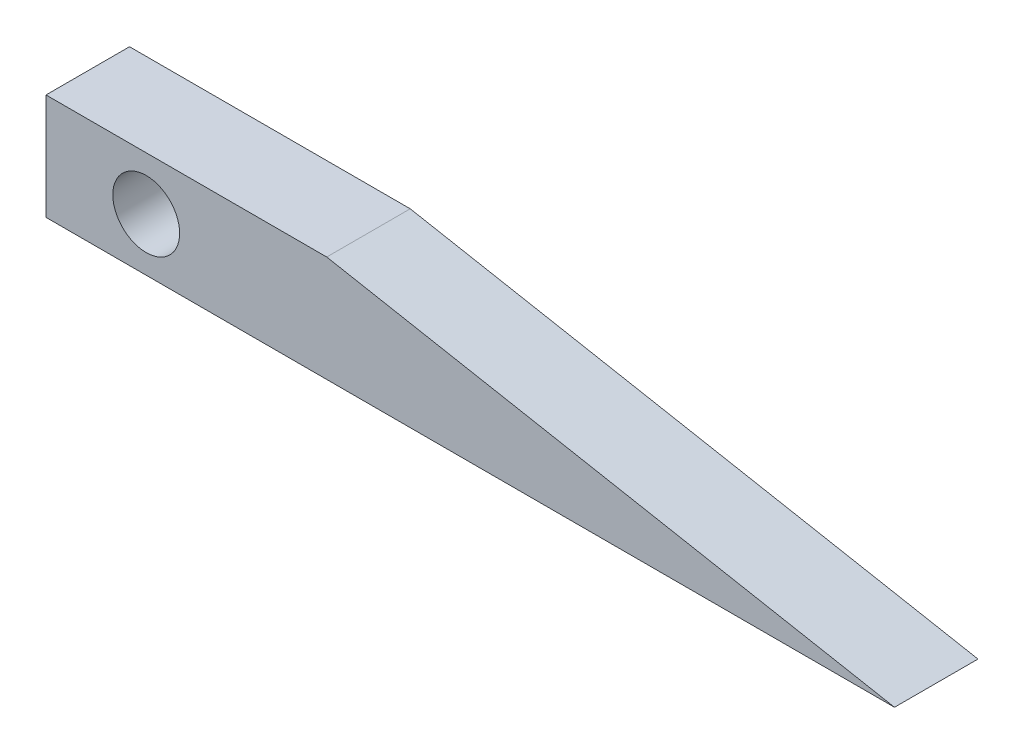
SolidWorks part; units mm, degrees
ref_plane "Front Plane" through (0, 0, 0) normal (0, 0, 1) x (1, 0, 0)
ref_plane "Top Plane" through (0, 0, 0) normal (0, 1, 0) x (1, 0, 0)
ref_plane "Right Plane" through (0, 0, 0) normal (1, 0, 0) x (0, 0, -1)
sketch "Sketch1" plane through (0, 0, 0) normal (0, 0, 1) x (1, 0, 0)
  line L5 (0, 6.35) -> (50.8, 6.35)
  line L6 (0, 6.35) -> (0, 0)
  line L7 (0, 0) -> (50.8, 0)
  line L8 (50.8, 6.35) -> (50.8, 0)
  dimension "D1" = 50.8
  dimension "D2" = 6.35
extrude "Boss-Extrude1" add sketch "Sketch1" along normal blind 5
sketch "Sketch2" plane through (0, 0, 0) normal (0, 0, -1) x (-1, 0, 0)
  line L0 (-50.8, 6.35) -> (0, 6.35) construction
  line L2 (0, 6.35) -> (0, 0) construction
  circle A0 centre (-6, 3.175) radius 2
  dimension "D1" = 4
  dimension "D2" = 3.175
  dimension "D3" = 6
extrude "Cut-Extrude1" cut sketch "Sketch2" against normal up to surface (5 mm away) up to face at (25.4, 3.175, 5)
sketch "Sketch3" plane through (0, 0, 0) normal (0, 0, -1) x (-1, 0, 0)
  line L0 (-50.8, 0) -> (-16.807, 6.35)
  line L1 (-50.8, 6.35) -> (0, 6.35) construction
  line L2 (-16.807, 6.35) -> (-50.8, 6.35)
  line L3 (-50.8, 6.35) -> (-50.8, 0)
  dimension "D1" = 34.581
extrude "Cut-Extrude2" cut sketch "Sketch3" against normal up to surface (5 mm away) up to face at (8, 3.175, 5)
